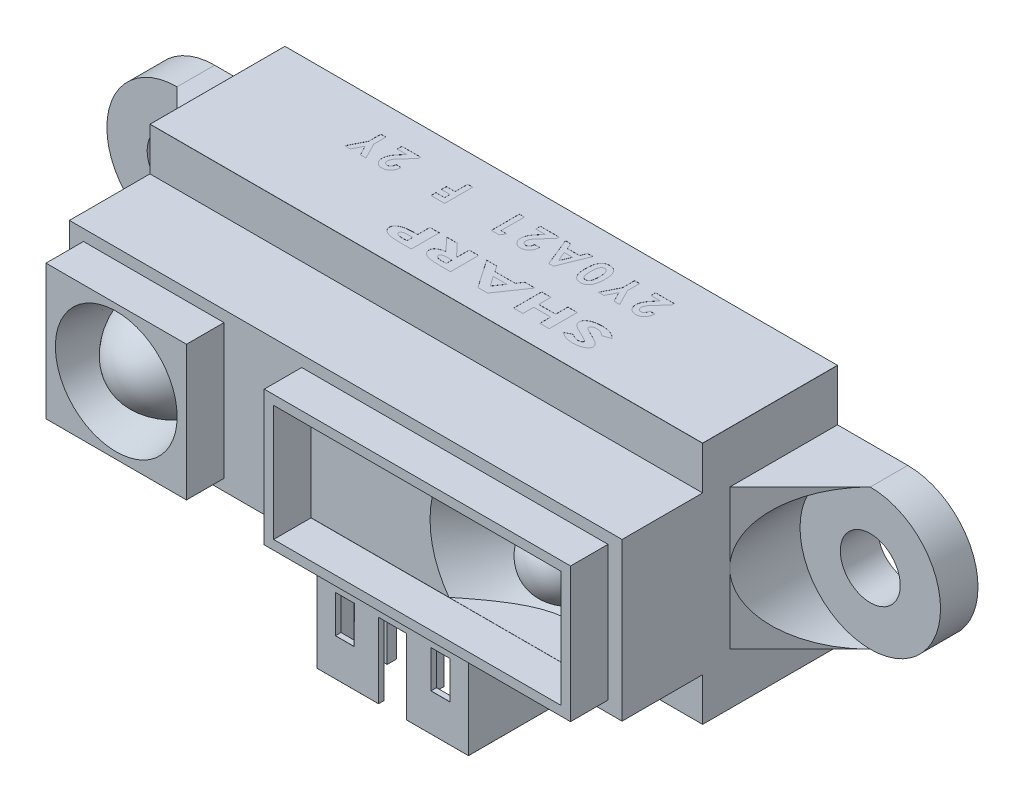
SolidWorks part; units mm, degrees
ref_plane "Front Plane" through (0, 0, 0) normal (0, 0, 1) x (1, 0, 0)
ref_plane "Top Plane" through (0, 0, 0) normal (0, 1, 0) x (1, 0, 0)
ref_plane "Right Plane" through (0, 0, 0) normal (1, 0, 0) x (0, 0, -1)
sketch "Sketch1" plane through (0, 0, 0) normal (0, 0, 1) x (1, 0, 0)
  line L0 (-18.5, 3.75) -> (-14.75, 3.75)
  line L1 (-14.75, -6.5) -> (14.75, -6.5)
  line L2 (-14.75, -6.5) -> (-14.75, -3.75)
  line L3 (-14.75, 6.5) -> (14.75, 6.5)
  line L4 (14.75, -6.5) -> (14.75, -3.75)
  line L5 (0, 0) -> (14.75, 6.5) construction
  line L6 (-14.75, 6.5) -> (0, 0) construction
  line L7 (-18.5, -3.75) -> (-14.75, -3.75)
  line L8 (18.5, -3.75) -> (14.75, -3.75)
  line L9 (18.5, 3.75) -> (14.75, 3.75)
  line L10 (-14.75, 3.75) -> (-14.75, 6.5)
  line L11 (14.75, 3.75) -> (14.75, 6.5)
  arc A0 (-18.5, 3.75) -> (-18.5, -3.75) centre (-18.5, 0) ccw
  arc A1 (18.5, -3.75) -> (18.5, 3.75) centre (18.5, 0) ccw
  circle A2 centre (-18.5, 0) radius 1.6
  circle A3 centre (18.5, 0) radius 1.6
  point P4 (0, 0)
  dimension "D2" = 37
  dimension "D3" = 18.5
  dimension "D4" = 7.5
  dimension "D5" = 7.5
  dimension "D7" = 3.2
  dimension "D8" = 3.2
  dimension "D1" = 29.5
  dimension "D6" = 13
extrude "Boss-Extrude1" add sketch "Sketch1" along normal blind 13.5
sketch "Sketch3" plane through (0, 0, 0) normal (0, 0, -1) x (-1, 0, 0)
  circle A0 centre (-18.5, 0) radius 3.75
  circle A1 centre (18.5, 0) radius 3.75
extrude "Cut-Extrude1" cut sketch "Sketch3" against normal through all from offset 2 offset against normal yes
sketch "Sketch4" plane through (0, -3.75, 0) normal (0, -1, 0) x (1, 0, 0)
  line L0 (22.25, 2) -> (18.5, 2)
  line L1 (18.5, 2) -> (14.75, 5.75)
  line L2 (14.75, 13.5) -> (14.75, 0) construction
  line L3 (14.75, 5.75) -> (14.75, 13.5)
  line L4 (14.75, 13.5) -> (22.25, 13.5)
  line L5 (22.25, 13.5) -> (22.25, 2)
  line L6 (-22.25, 2) -> (-18.5, 2)
  line L7 (-18.5, 2) -> (-14.75, 5.75)
  line L8 (-14.75, 13.5) -> (-14.75, 0) construction
  line L9 (-14.75, 5.75) -> (-14.75, 13.5)
  line L10 (-14.75, 13.5) -> (-22.25, 13.5)
  line L11 (-22.25, 13.5) -> (-22.25, 2)
  line L12 (14.75, 13.5) -> (14.75, 0) construction
  dimension "D1" = 45
  dimension "D2" = 45
extrude "Cut-Extrude2" cut sketch "Sketch4" against normal through all
sketch "Sketch5" plane through (0, 0, 13.5) normal (0, 0, 1) x (1, 0, 0)
  line L0 (14.75, -6.5) -> (14.75, 6.5) construction
  line L1 (-14.75, 6.5) -> (14.75, 6.5)
  line L2 (-14.75, 6.5) -> (-14.75, 4.2)
  line L3 (-14.75, 4.2) -> (14.75, 4.2)
  line L4 (14.75, 6.5) -> (14.75, 4.2)
  line L6 (-14.75, -6.5) -> (14.75, -6.5)
  line L7 (-14.75, -6.5) -> (-14.75, -4.2)
  line L8 (-14.75, -4.2) -> (14.75, -4.2)
  line L9 (14.75, -6.5) -> (14.75, -4.2)
  dimension "D1" = 8.4
  dimension "D2" = 4.2
extrude "Cut-Extrude3" cut sketch "Sketch5" along normal through all from offset 6.3 offset against normal yes
sketch "Sketch6" plane through (0, 0, 13.5) normal (0, 0, 1) x (1, 0, 0)
  line L0 (-14.75, 4.2) -> (-14.75, -4.2) construction
  line L1 (-14, -3.6) -> (-6.5, -3.6)
  line L2 (-14, -3.6) -> (-14, 3.6)
  line L3 (-14, 3.6) -> (-6.5, 3.6)
  line L4 (14, -3.6) -> (14, 3.6)
  line L5 (-14, -3.6) -> (14, 3.6) construction
  line L6 (-14, 3.6) -> (14, -3.6) construction
  line L7 (-6.5, 3.6) -> (-6.5, -3.6)
  line L8 (-2.35, 3.6) -> (-2.35, -3.6)
  line L9 (-2.35, 3.6) -> (14, 3.6)
  line L10 (-2.35, -3.6) -> (14, -3.6)
  line L12 (-14.75, -4.2) -> (14.75, -4.2)
  line L13 (-14.75, -4.2) -> (-14.75, 4.2)
  line L14 (-14.75, 4.2) -> (14.75, 4.2)
  line L15 (14.75, -4.2) -> (14.75, 4.2)
  line L16 (-14.75, -4.2) -> (14.75, 4.2) construction
  line L17 (-14.75, 4.2) -> (14.75, -4.2) construction
  point P0 (0, 0)
  point P12 (0, 0)
  dimension "D1" = 7.2
  dimension "D2" = 0.75
  dimension "D3" = 7.5
  dimension "D4" = 4.15
  dimension "D5" = 16.35
extrude "Cut-Extrude4" cut sketch "Sketch6" along normal through all from offset 2 offset against normal yes
sketch "Sketch7" plane through (0, 0, 13.5) normal (0, 0, 1) x (1, 0, 0)
  line L0 (-6.5, -3.6) -> (-6.5, 3.6) construction
  line L1 (-6.5, 3.6) -> (-14, 3.6) construction
  circle A0 centre (-10.25, 0) radius 3.25
  point P4 (-6.5, 0)
  point P8 (-10.25, 3.6)
  dimension "D1" = 6.5
extrude "Cut-Extrude5" cut sketch "Sketch7" against normal blind 3 draft 10
sketch "Sketch8" plane through (0, 0, 0) normal (0, 1, 0) x (1, 0, 0)
  line L0 (-10.25, -10.5) -> (-10.25, -17.4091) construction
  line L1 (-12.971, -10.5) -> (-7.529, -10.5) construction
  line L2 (-10.25, -10.5) -> (-7.529, -10.5)
  line L3 (-14, -13.5) -> (-6.5, -13.5) construction
  line L4 (-13.25, -13.5) -> (-7.25, -13.5) construction
  line L5 (-7.529, -13.5) -> (-7.529, -7.5) construction
  line L6 (-10.25, -10.5) -> (-10.25, -13.5)
  spline S0 degree 3 poles (-7.529, -10.5) (-7.529, -11.5) (-8.5833, -13.5) (-10.25, -13.5) knots 0 0 0 0 1 1 1 1
  dimension "D1" = 5
  dimension "D2" = 3
  dimension "D3" = 90
  dimension "D4" = 90
revolve "Revolve1" add sketch "Sketch8" angle 360 about L0
sketch "Sketch9" plane through (0, 0, 13.5) normal (0, 0, 1) x (1, 0, 0)
  line L0 (14, 3.6) -> (-2.35, 3.6) construction
  line L1 (-1.85, -3.1) -> (13.5, -3.1)
  line L2 (-1.85, -3.1) -> (-1.85, 3.1)
  line L3 (-1.85, 3.1) -> (13.5, 3.1)
  line L4 (13.5, -3.1) -> (13.5, 3.1)
  line L5 (-2.35, 3.6) -> (-2.35, -3.6) construction
  line L6 (14, -3.6) -> (14, 3.6) construction
  line L7 (-2.35, -3.6) -> (14, -3.6) construction
  dimension "D1" = 0.5
  dimension "D2" = 0.5
  dimension "D3" = 0.5
  dimension "D4" = 0.5
extrude "Cut-Extrude6" cut sketch "Sketch9" against normal blind 2
sketch "Sketch10" plane through (0, 0, 11.5) normal (0, 0, 1) x (1, 0, 0)
  line L0 (-14.75, 4.2) -> (-14.75, -4.2) construction
  line L1 (14, -3.6) -> (14, 3.6) construction
  line L7 (13.5, -3.1) -> (13.5, 3.1) construction
  circle A2 centre (9.75, 0) radius 2.25
  point P7 (14, 0)
  point P17 (13.5, 0)
  dimension "D2" = 4.5
  dimension "D1" = 24.5
sketch "Sketch12" plane through (0, 0, 0) normal (0, 0, -1) x (-1, 0, 0)
  line L0 (14.75, -6.5) -> (-14.75, -6.5) construction
  line L1 (5.05, -6.5) -> (-5.05, -6.5)
  line L2 (5.05, -6.5) -> (5.05, -12.4)
  line L3 (5.05, -12.4) -> (-5.05, -12.4)
  line L4 (-5.05, -6.5) -> (-5.05, -12.4)
  point P6 (0, -6.5)
  dimension "D1" = 10.1
  dimension "D2" = 5.9
extrude "Boss-Extrude2" add sketch "Sketch12" against normal blind 1.2 from offset 3.3 offset against normal yes
sketch "Sketch13" plane through (0, -6.5, 0) normal (0, -1, 0) x (1, 0, 0)
  line L0 (-14.75, 7.2) -> (14.75, 7.2) construction
  line L1 (5.05, 4.5) -> (-5.05, 4.5)
  line L2 (5.05, 4.5) -> (5.05, 7.2)
  line L3 (5.05, 7.2) -> (-5.05, 7.2)
  line L4 (-5.05, 4.5) -> (-5.05, 7.2)
extrude "Cut-Extrude8" cut sketch "Sketch13" against normal up to surface (2.3 mm away) up to face at (0, -4.2, 9.35)
sketch "Sketch14" plane through (0, -4.2, 0) normal (0, -1, 0) x (1, 0, 0)
  line L0 (5.05, 4.5) -> (-5.05, 4.5) construction
  line L1 (-4.05, 4.5) -> (4.05, 4.5)
  line L2 (-4.05, 4.5) -> (-4.05, 9)
  line L3 (-4.05, 9) -> (4.05, 9)
  line L4 (4.05, 4.5) -> (4.05, 9)
  line L5 (-5.05, 7.2) -> (-5.05, 4.5) construction
  line L6 (-3.75, 4.8) -> (3.75, 4.8)
  line L7 (-3.75, 4.8) -> (-3.75, 8.7)
  line L8 (-3.75, 8.7) -> (3.75, 8.7)
  line L9 (3.75, 4.8) -> (3.75, 8.7)
  line L10 (-2.79, 7) -> (-2.29, 7)
  line L11 (-2.79, 7) -> (-2.79, 6.5)
  line L12 (-2.79, 6.5) -> (-2.29, 6.5)
  line L13 (-2.29, 7) -> (-2.29, 6.5)
  line L14 (-0.25, 7) -> (0.25, 7)
  line L15 (-0.25, 7) -> (-0.25, 6.5)
  line L16 (-0.25, 6.5) -> (0.25, 6.5)
  line L17 (0.25, 7) -> (0.25, 6.5)
  line L18 (2.29, 7) -> (2.79, 7)
  line L19 (2.29, 7) -> (2.29, 6.5)
  line L20 (2.29, 6.5) -> (2.79, 6.5)
  line L21 (2.79, 7) -> (2.79, 6.5)
  point P22 (0, 4.5)
  point P24 (0, 4.8)
  point P25 (0, 6.5)
  point P28 (-2.29, 6.75)
  point P29 (-0.25, 6.75)
  point P30 (2.29, 6.75)
  point P31 (-3.75, 6.75)
  line M23 (-5.05, 4.5) -> (5.05, 4.5)
  dimension "D1" = 4.5
  dimension "D2" = 1
  dimension "D3" = 0.3
  dimension "D4" = 0.3
  dimension "D5" = 0.3
  dimension "D6" = 0.5
  dimension "D7" = 0.5
  dimension "D8" = 0.5
  dimension "D9" = 0.5
  dimension "D10" = 0.5
  dimension "D11" = 0.5
  dimension "D12" = 2.54
  dimension "D13" = 2.54
extrude "Boss-Extrude3" add sketch "Sketch14" along normal through all contours L4 L3 L2 L9 L6 L7 L8 M23 | L17 L14 L15 L16 | L21 L20 L19 L18 | L12 L13 L10 L11
sketch "Sketch15" plane through (0, -4.2, 0) normal (0, -1, 0) x (1, 0, 0)
  line L1 (-3.75, 4.8) -> (3.75, 4.8)
  line L2 (-3.75, 4.8) -> (-3.75, 8.7)
  line L3 (-3.75, 8.7) -> (3.75, 8.7)
  line L4 (3.75, 4.8) -> (3.75, 8.7)
extrude "Boss-Extrude4" add sketch "Sketch15" along normal blind 1 from offset 1.5
sketch "Sketch16" plane through (0, 0, 9) normal (0, 0, 1) x (1, 0, 0)
  line L0 (-4.05, -4.2) -> (-4.05, -4.8602)
  line L1 (-4.05, -12.4) -> (-4.05, -4.2) construction
  line L2 (-4.05, -4.8602) -> (-3.55, -4.8602)
  line L3 (-3.55, -4.8602) -> (-3.55, -5.7602)
  line L4 (-3.55, -5.7602) -> (3.55, -5.7602)
  line L5 (3.55, -5.7602) -> (3.55, -4.8)
  line L6 (3.55, -4.8) -> (4.05, -4.8)
  line L7 (4.05, -12.4) -> (4.05, -4.2) construction
  line L8 (4.05, -4.8) -> (4.05, -4.2)
  line L9 (-4.05, -12.4) -> (-4.05, -4.2) construction
  line L10 (-4.05, -4.2) -> (4.05, -4.2)
  dimension "D1" = 0.6
  dimension "D2" = 0.9
  dimension "D3" = 0.5
  dimension "D4" = 0.5
extrude "Cut-Extrude9" cut sketch "Sketch16" against normal up to surface (4.5 mm away) up to face at (-4.65, -7.94, 4.5)
sketch "Sketch17" plane through (0, -12.4, 0) normal (0, -1, 0) x (-1, 0, 0)
  line L0 (4.05, -4.5) -> (4.05, -9) construction
  line L1 (-4.05, -4.5) -> (4.05, -4.5)
  line L2 (-4.05, -4.5) -> (-4.05, -4.6)
  line L3 (-4.05, -4.6) -> (4.05, -4.6)
  line L4 (4.05, -4.5) -> (4.05, -4.6)
  point P7 (4.05, -4.55)
  dimension "D1" = 0.05
extrude "Cut-Extrude10" cut sketch "Sketch17" against normal blind 0.1
chamfer "Chamfer3" distance 0.05 12 edges at (2.29, -12.4, 6.75) (2.54, -12.4, 7) (2.79, -12.4, 6.75) (2.54, -12.4, 6.5) (-0.25, -12.4, 6.75) (0, -12.4, 7) (0.25, -12.4, 6.75) (0, -12.4, 6.5) (-2.79, -12.4, 6.75) (-2.54, -12.4, 7) (-2.29, -12.4, 6.75) (-2.54, -12.4, 6.5)
sketch "Sketch18" plane through (0, 0, 9) normal (0, 0, 1) x (1, 0, 0)
  line L0 (-4.05, -12.4) -> (4.05, -12.4) construction
  line L1 (-0.75, -12.4) -> (0.75, -12.4)
  line L2 (-0.75, -12.4) -> (-0.75, -8.4)
  line L3 (-0.75, -8.4) -> (0.75, -8.4)
  line L4 (0.75, -12.4) -> (0.75, -8.4)
  line L5 (-4.05, -12.3) -> (-4.05, -4.8602) construction
  line L6 (-3.05, -8.4) -> (-2.05, -8.4)
  line L7 (-3.05, -8.4) -> (-3.05, -10.4)
  line L8 (-3.05, -10.4) -> (-2.05, -10.4)
  line L9 (-2.05, -8.4) -> (-2.05, -10.4)
  line L10 (2.05, -8.4) -> (3.05, -8.4)
  line L11 (2.05, -8.4) -> (2.05, -10.4)
  line L12 (2.05, -10.4) -> (3.05, -10.4)
  line L13 (3.05, -8.4) -> (3.05, -10.4)
  line L14 (4.05, -12.4) -> (4.05, -4.8) construction
  point P14 (0, -12.4)
  dimension "D1" = 2
  dimension "D2" = 1
  dimension "D3" = 1
  dimension "D4" = 2
  dimension "D5" = 2
  dimension "D6" = 1
  dimension "D7" = 2
  dimension "D8" = 1
  dimension "D9" = 1.5
  dimension "D10" = 4
extrude "Cut-Extrude11" cut sketch "Sketch18" against normal up to surface (0.3 mm away) up to face at (0, -9.55, 8.7)
fillet "Fillet1" radius 0.005 55 edges at (-14.75, 6.5, 3.6) (14.75, 6.5, 3.6) (0, 6.5, 7.2) (0, -12.3, 4.5) (-3.8, -4.8602, 4.5) (-3.8, -4.8602, 9) (13.5, 0, 11.5) (5.825, -3.1, 11.5) (-2.55, -10.4, 8.7) (-3.05, -9.4, 8.7) (-2.55, -8.4, 8.7) (-2.05, -9.4, 8.7) (2.55, -10.4, 8.7) (2.05, -9.4, 8.7) (2.55, -8.4, 8.7) (3.05, -9.4, 8.7) (-3.75, -9.55, 8.7) (0, -6.7, 8.7) (3.75, -9.55, 8.7) (2.25, -12.4, 8.7) (3.75, -12.4, 6.75) (0, -12.4, 4.8) (-3.75, -12.4, 6.75) (-2.25, -12.4, 8.7) (4.05, -8.6, 9) (3.8, -4.8, 9) (3.55, -5.2801, 9) (0, -5.7602, 9) (-3.55, -5.3102, 9) (-4.05, -8.5801, 4.5) (-4.05, -4.8602, 6.75) (-4.05, -8.6301, 9) (-4.05, -12.4, 6.8) (-2.4, -12.4, 9) (0.75, -10.4, 9) (0, -8.4, 9) (-0.75, -10.4, 9) (-0.75, -12.4, 8.85) (-0.75, -10.4, 8.7) (0, -8.4, 8.7) (0.75, -10.4, 8.7) (0.75, -12.4, 8.85) (2.4, -12.4, 9) (4.05, -12.4, 6.8) (0, -12.4, 4.6) (-4.05, -12.35, 4.6) (-4.05, -12.3, 4.55) (-2.55, -10.4, 9) (-2.05, -9.4, 9) (-2.55, -8.4, 9) (-3.05, -9.4, 9) (2.55, -10.4, 9) (3.05, -9.4, 9) (2.55, -8.4, 9) (2.05, -9.4, 9)
sketch "Sketch19" plane through (0, 6.5, 0) normal (0, 1, 0) x (1, 0, 0)
  line L0 (-8.6216, -1.5) -> (7.745, -1.5) construction
  line L1 (-3.8692, -4.5) -> (7.745, -4.5) construction
  line L2 (14.745, -7.195) -> (14.745, 0) construction
  line L3 (14.745, 0) -> (-14.745, 0) construction
  text T0 "<b>SHARP</b>" font "Century Gothic" height 1.5
  text T1 "<b>2Y0A21  F  2Y</b>" font "Century Gothic" height 1.5
  point P11 (-0.4383, -1.5)
  dimension "D1" = 7
  dimension "D2" = 7
  dimension "D3" = 1.5
  dimension "D4" = 3
extrude "Cut-Extrude12" cut sketch "Sketch19" against normal blind 0.005
extrude "Cut-Extrude13" cut sketch "Sketch10" against normal blind 3
sketch "Sketch21" plane through (0, 0, 0) normal (0, 1, 0) x (1, 0, 0)
  line L0 (9.75, -8.5) -> (9.75, -21.6727) construction
  line L1 (7.5, -8.5) -> (12, -8.5) construction
  line L2 (-2.35, -11.5) -> (14, -11.5) construction
  line L3 (4.5, -11.5) -> (9.75, -11.5)
  line L4 (9.75, -8.5) -> (7.5, -8.5)
  line L5 (7.5, -8.5) -> (4.5, -11.5)
  line L6 (9.75, -8.5) -> (9.75, -11.5)
  dimension "D1" = 2.25
  dimension "D2" = 45
sketch "Sketch22" plane through (0, 0, 8.5) normal (0, 0, 1) x (1, 0, 0)
  circle A0 centre (9.75, 0) radius 2.25
sweep "Cut-Sweep1" cut profiles "Sketch21" path "Sketch22"
sketch "Sketch24" plane through (0, 0, 11.5) normal (0, 0, 1) x (1, 0, 0)
  line L0 (4.0461, 3.1) -> (4.0461, 4.2)
  line L1 (5.513, 3.1) -> (-1.85, 3.1) construction
  line L2 (6.6, 4.2) -> (-14.75, 4.2) construction
  line L3 (4.0461, 4.2) -> (14.75, 4.2)
  line L4 (14.75, 4.2) -> (14.75, -4.2)
  line L5 (14.75, -4.2) -> (4.0461, -4.2)
  line L6 (-14.75, -4.2) -> (6.6, -4.2) construction
  line L7 (4.0461, -4.2) -> (4.0461, -3.095)
  line L8 (-1.85, -3.095) -> (5.5093, -3.095) construction
  line L9 (4.0461, -3.095) -> (13.5, -3.095)
  line L10 (13.5, -3.095) -> (13.5, 3.1)
  line L11 (13.5, 3.1) -> (4.0461, 3.1)
  line L13 (13.5, 3.1) -> (13.5, -3.1) construction
extrude "Boss-Extrude5" add sketch "Sketch24" against normal up to surface (4.3 mm away) up to face at (0, 5.3475, 7.2)
sketch "Sketch25" plane through (0, 0, 0) normal (0, 1, 0) x (1, 0, 0)
  line L0 (9.75, -8.5) -> (9.75, -25.3837) construction
  line L1 (7.5, -8.5) -> (12, -8.5) construction
  line L2 (9.75, -8.5) -> (12, -8.5)
  line L3 (14, -11.5) -> (-2.35, -11.5) construction
  line L4 (12, -11.5) -> (12, -5.5) construction
  line L5 (3.75, -11.5) -> (15.75, -11.5) construction
  line L6 (9.75, -8.5) -> (9.75, -11.5)
  spline S0 degree 3 poles (12, -8.5) (12, -9.5) (11.4167, -11.5) (9.75, -11.5) knots 0 0 0 0 1 1 1 1
  dimension "D1" = 3
  dimension "D2" = 5
  dimension "D3" = 90
  dimension "D4" = 90
revolve "Revolve4" add sketch "Sketch25" angle 360 about L0
